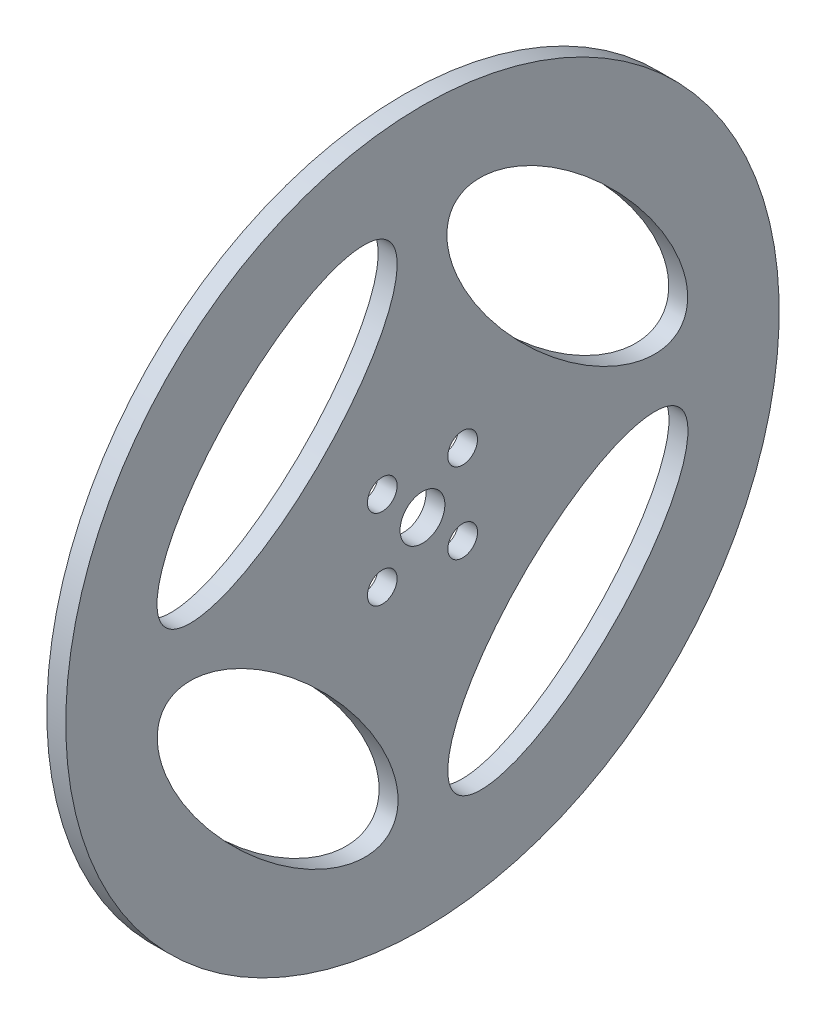
SolidWorks part; units mm, degrees
material "Balsaholz"
ref_plane "Ebene vorne" through (0, 0, 0) normal (0, 0, 1) x (1, 0, 0)
ref_plane "Ebene oben" through (0, 0, 0) normal (0, 1, 0) x (1, 0, 0)
ref_plane "Ebene rechts" through (0, 0, 0) normal (1, 0, 0) x (0, 0, -1)
sketch "Skizze1" plane through (0, 0, 0) normal (0, 0, 1) x (1, 0, 0)
  line L0 (-38.0534, 66.25) -> (-41.0534, 66.25)
  line L2 (-41.0534, 13.3) -> (-38.0534, 13.3)
  line L5 (-41.0534, 13.3) -> (-41.0534, 66.25)
  line L8 (-17.6629, 9.75) -> (-37.0534, 9.75) construction
  line L12 (-38.0534, 13.3) -> (-38.0534, 66.25)
  line L25 (-41.0534, 28.75) -> (-41.0534, 26.8663) construction
  dimension "D5" = 113
  dimension "D2" = 7.1
  dimension "D6" = 3
revolve "Rotation1" add sketch "Skizze1" angle 360 about L8
hole_wizard "Ø4.7 (4.7) Durchmesser Bohrung1" positions "Skizze3" profile "Skizze4" hole size "Ø4.7" standard "DIN" end condition through all
sketch "Skizze3" plane through (-41.0534, 11.9687, 19.8689) normal (-1, 0, 0) x (0, 0, 1)
  point P0 (-13.505, -8.5827)
  point P3 (-26.2329, -8.5827)
  point P6 (-26.2329, 4.1452)
  point P9 (-13.505, 4.1452)
sketch "Skizze4" plane through (-41.0534, 3.386, 6.364) normal (0, 1, 0) x (0, 0, 1)
  line L0 (0, 0) -> (0, 3)
  line L1 (0, 3) -> (2.35, 3)
  line L2 (2.35, 3) -> (2.35, 0)
  line L5 (2.35, 0) -> (0, 0)
  line L11 (0, -6.35) -> (0, 107.95) construction
  dimension "Bohrerdurchmesser" = 4.7
  dimension "Bohrungstiefe" = 3
sketch "Skizze5" plane through (-38.0534, 0, 0) normal (1, 0, 0) x (0, 0, -1)
  line L0 (-15.9451, 25.6246) -> (-23.0273, 32.6845) construction
  line L1 (6.364, 3.386) -> (-6.2453, 15.9555) construction
  circle A0 centre (0, 9.75) radius 22.5 construction
  ellipse E0 centre (-23.0273, 32.6845) end of major axis (-5.3776, 50.3901) minor radius 10
  dimension "D1" = 45
  dimension "D3" = 50
  dimension "D4" = 20
extrude "Schnitt-Linear austragen1" cut sketch "Skizze5" against normal up to next (3 mm away)
pattern_circular "Kreismuster1" count 4 over 360 of "Schnitt-Linear austragen1"
ref_plane "Plane1" through (-41.0534, 0, 0) normal (-1, 0, 0) x (0, 0, 1)
